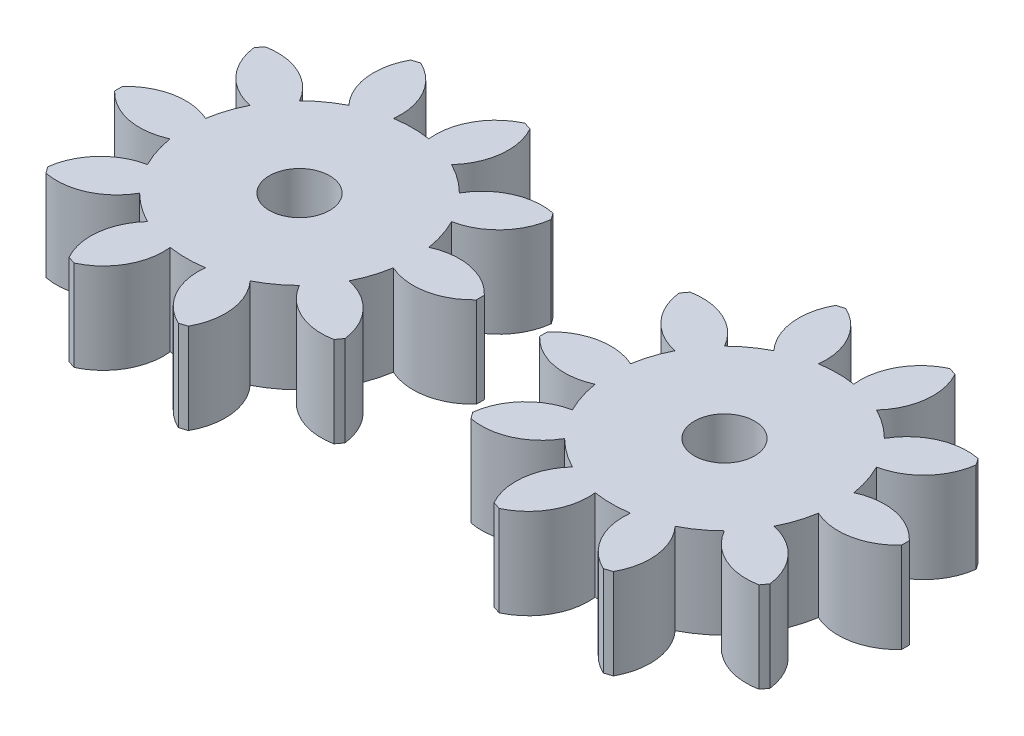
SolidWorks part; units mm, degrees
ref_plane "Front Plane" through (0, 0, 0) normal (0, 0, 1) x (1, 0, 0)
ref_plane "Top Plane" through (0, 0, 0) normal (0, 1, 0) x (1, 0, 0)
ref_plane "Right Plane" through (0, 0, 0) normal (1, 0, 0) x (0, 0, -1)
sketch "Sketch2" plane through (0, 0, 0) normal (0, 1, 0) x (1, 0, 0)
  point P0 (0, 0)
  circle B0 centre (15.9251, 69.1831) radius 4
  arc B1 (39.9193, 68.6545) -> (39.9193, 69.7117) centre (15.9251, 69.1831) ccw
  arc B2 (30.7381, 66.8284) -> (39.9193, 68.6545) centre (34.0631, 74.1047) ccw
  arc B3 (29.2931, 62.3812) -> (30.7381, 66.8284) centre (15.9251, 69.1831) ccw
  arc B4 (35.6475, 55.5074) -> (29.2931, 62.3812) centre (27.7062, 54.5402) ccw
  arc B5 (35.0261, 54.652) -> (35.6475, 55.5074) centre (15.9251, 69.1831) ccw
  arc B6 (26.525, 58.5713) -> (35.0261, 54.652) centre (33.4919, 62.5036) ccw
  arc B7 (22.742, 55.8227) -> (26.525, 58.5713) centre (15.9251, 69.1831) ccw
  arc B8 (23.8425, 46.5267) -> (22.742, 55.8227) centre (16.8493, 50.412) ccw
  arc B9 (22.837, 46.2) -> (23.8425, 46.5267) centre (15.9251, 69.1831) ccw
  arc B10 (18.2631, 54.3675) -> (22.837, 46.2) centre (26.2108, 53.4537) ccw
  arc B11 (13.5871, 54.3675) -> (18.2631, 54.3675) centre (15.9251, 69.1831) ccw
  arc B12 (9.0132, 46.2) -> (13.5871, 54.3675) centre (5.6394, 53.4537) ccw
  arc B13 (8.0078, 46.5267) -> (9.0132, 46.2) centre (15.9251, 69.1831) ccw
  arc B14 (9.1082, 55.8227) -> (8.0078, 46.5267) centre (15.0009, 50.412) ccw
  arc B15 (5.3252, 58.5713) -> (9.1082, 55.8227) centre (15.9251, 69.1831) ccw
  arc B16 (-3.1759, 54.652) -> (5.3252, 58.5713) centre (-1.6417, 62.5036) ccw
  arc B17 (-3.7973, 55.5074) -> (-3.1759, 54.652) centre (15.9251, 69.1831) ccw
  arc B18 (2.5571, 62.3812) -> (-3.7973, 55.5074) centre (4.144, 54.5402) ccw
  arc B19 (1.1121, 66.8284) -> (2.5571, 62.3812) centre (15.9251, 69.1831) ccw
  arc B20 (-8.0691, 68.6545) -> (1.1121, 66.8284) centre (-2.2129, 74.1047) ccw
  arc B21 (-8.0691, 69.7117) -> (-8.0691, 68.6545) centre (15.9251, 69.1831) ccw
  arc B22 (1.1121, 71.5378) -> (-8.0691, 69.7117) centre (-2.2129, 64.2615) ccw
  arc B23 (2.5571, 75.985) -> (1.1121, 71.5378) centre (15.9251, 69.1831) ccw
  arc B24 (-3.7973, 82.8589) -> (2.5571, 75.985) centre (4.144, 83.826) ccw
  arc B25 (-3.1759, 83.7142) -> (-3.7973, 82.8589) centre (15.9251, 69.1831) ccw
  arc B26 (5.3252, 79.795) -> (-3.1759, 83.7142) centre (-1.6417, 75.8627) ccw
  arc B27 (9.1082, 82.5435) -> (5.3252, 79.795) centre (15.9251, 69.1831) ccw
  arc B28 (8.0078, 91.8396) -> (9.1082, 82.5435) centre (15.0009, 87.9542) ccw
  arc B29 (9.0132, 92.1663) -> (8.0078, 91.8396) centre (15.9251, 69.1831) ccw
  arc B30 (13.5871, 83.9988) -> (9.0132, 92.1663) centre (5.6394, 84.9125) ccw
  arc B31 (18.2631, 83.9988) -> (13.5871, 83.9988) centre (15.9251, 69.1831) ccw
  arc B32 (22.837, 92.1663) -> (18.2631, 83.9988) centre (26.2108, 84.9125) ccw
  arc B33 (23.8425, 91.8396) -> (22.837, 92.1663) centre (15.9251, 69.1831) ccw
  arc B34 (22.742, 82.5435) -> (23.8425, 91.8396) centre (16.8493, 87.9542) ccw
  arc B35 (26.525, 79.795) -> (22.742, 82.5435) centre (15.9251, 69.1831) ccw
  arc B36 (35.0261, 83.7142) -> (26.525, 79.795) centre (33.4919, 75.8627) ccw
  arc B37 (35.6475, 82.8589) -> (35.0261, 83.7142) centre (15.9251, 69.1831) ccw
  arc B38 (29.2931, 75.985) -> (35.6475, 82.8589) centre (27.7062, 83.826) ccw
  arc B39 (30.7381, 71.5378) -> (29.2931, 75.985) centre (15.9251, 69.1831) ccw
  arc B40 (39.9193, 69.7117) -> (30.7381, 71.5378) centre (34.0631, 64.2615) ccw
  circle B41 centre (72.3122, 69.1831) radius 4
  arc B42 (96.3064, 68.6545) -> (96.3064, 69.7117) centre (72.3122, 69.1831) ccw
  arc B43 (87.1252, 66.8284) -> (96.3064, 68.6545) centre (90.4502, 74.1047) ccw
  arc B44 (85.6802, 62.3812) -> (87.1252, 66.8284) centre (72.3122, 69.1831) ccw
  arc B45 (92.0346, 55.5074) -> (85.6802, 62.3812) centre (84.0933, 54.5402) ccw
  arc B46 (91.4132, 54.652) -> (92.0346, 55.5074) centre (72.3122, 69.1831) ccw
  arc B47 (82.9121, 58.5713) -> (91.4132, 54.652) centre (89.879, 62.5036) ccw
  arc B48 (79.1291, 55.8227) -> (82.9121, 58.5713) centre (72.3122, 69.1831) ccw
  arc B49 (80.2295, 46.5267) -> (79.1291, 55.8227) centre (73.2364, 50.412) ccw
  arc B50 (79.2241, 46.2) -> (80.2295, 46.5267) centre (72.3122, 69.1831) ccw
  arc B51 (74.6502, 54.3675) -> (79.2241, 46.2) centre (82.5979, 53.4537) ccw
  arc B52 (69.9742, 54.3675) -> (74.6502, 54.3675) centre (72.3122, 69.1831) ccw
  arc B53 (65.4003, 46.2) -> (69.9742, 54.3675) centre (62.0265, 53.4537) ccw
  arc B54 (64.3948, 46.5267) -> (65.4003, 46.2) centre (72.3122, 69.1831) ccw
  arc B55 (65.4953, 55.8227) -> (64.3948, 46.5267) centre (71.388, 50.412) ccw
  arc B56 (61.7123, 58.5713) -> (65.4953, 55.8227) centre (72.3122, 69.1831) ccw
  arc B57 (53.2112, 54.652) -> (61.7123, 58.5713) centre (54.7454, 62.5036) ccw
  arc B58 (52.5898, 55.5074) -> (53.2112, 54.652) centre (72.3122, 69.1831) ccw
  arc B59 (58.9442, 62.3812) -> (52.5898, 55.5074) centre (60.5311, 54.5402) ccw
  arc B60 (57.4992, 66.8284) -> (58.9442, 62.3812) centre (72.3122, 69.1831) ccw
  arc B61 (48.318, 68.6545) -> (57.4992, 66.8284) centre (54.1742, 74.1047) ccw
  arc B62 (48.318, 69.7117) -> (48.318, 68.6545) centre (72.3122, 69.1831) ccw
  arc B63 (57.4992, 71.5378) -> (48.318, 69.7117) centre (54.1742, 64.2615) ccw
  arc B64 (58.9442, 75.985) -> (57.4992, 71.5378) centre (72.3122, 69.1831) ccw
  arc B65 (52.5898, 82.8589) -> (58.9442, 75.985) centre (60.5311, 83.826) ccw
  arc B66 (53.2112, 83.7142) -> (52.5898, 82.8589) centre (72.3122, 69.1831) ccw
  arc B67 (61.7123, 79.795) -> (53.2112, 83.7142) centre (54.7454, 75.8627) ccw
  arc B68 (65.4953, 82.5435) -> (61.7123, 79.795) centre (72.3122, 69.1831) ccw
  arc B69 (64.3948, 91.8396) -> (65.4953, 82.5435) centre (71.388, 87.9542) ccw
  arc B70 (65.4003, 92.1663) -> (64.3948, 91.8396) centre (72.3122, 69.1831) ccw
  arc B71 (69.9742, 83.9988) -> (65.4003, 92.1663) centre (62.0265, 84.9125) ccw
  arc B72 (74.6502, 83.9988) -> (69.9742, 83.9988) centre (72.3122, 69.1831) ccw
  arc B73 (79.2241, 92.1663) -> (74.6502, 83.9988) centre (82.5979, 84.9125) ccw
  arc B74 (80.2295, 91.8396) -> (79.2241, 92.1663) centre (72.3122, 69.1831) ccw
  arc B75 (79.1291, 82.5435) -> (80.2295, 91.8396) centre (73.2364, 87.9542) ccw
  arc B76 (82.9121, 79.795) -> (79.1291, 82.5435) centre (72.3122, 69.1831) ccw
  arc B77 (91.4132, 83.7142) -> (82.9121, 79.795) centre (89.879, 75.8627) ccw
  arc B78 (92.0346, 82.8589) -> (91.4132, 83.7142) centre (72.3122, 69.1831) ccw
  arc B79 (85.6802, 75.985) -> (92.0346, 82.8589) centre (84.0933, 83.826) ccw
  arc B80 (87.1252, 71.5378) -> (85.6802, 75.985) centre (72.3122, 69.1831) ccw
  arc B81 (96.3064, 69.7117) -> (87.1252, 71.5378) centre (90.4502, 64.2615) ccw
sketch_block_instance "Block2-1"
sketch_block "Block2"
sketch_block_instance "Block2-2"
extrude "Boss-Extrude1" add sketch "Sketch2" along normal blind 12
